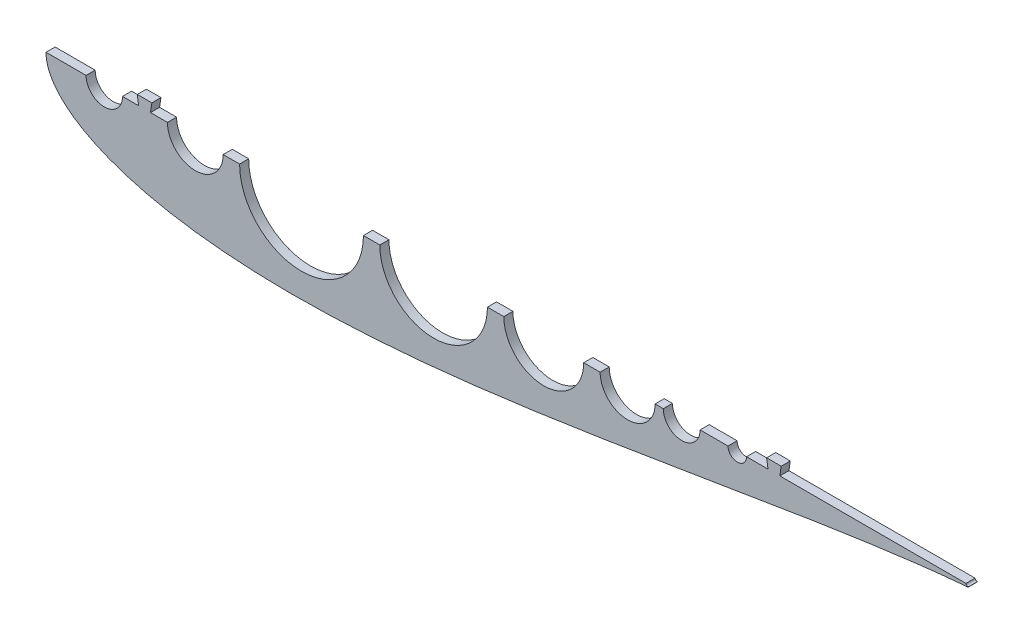
SolidWorks part; units mm, degrees
material "Beech"
ref_plane "Front Plane" through (0, 0, 0) normal (0, 0, 1) x (1, 0, 0)
ref_plane "Top Plane" through (0, 0, 0) normal (0, 1, 0) x (1, 0, 0)
ref_plane "Right Plane" through (0, 0, 0) normal (1, 0, 0) x (0, 0, -1)
curve "Curve4"
  spline degree 3 poles (100, 0, 0) (99.8498, 0.0023, 0) (99.4759, 0.008, 0) (99.1023, 0.0238, 0) (98.8789, 0.0332, 0) knots 0 0 0 0 0.401829 1 1 1 1
curve "Curve5"
  spline degree 3 poles (99.3714, -0.0082, 0) (100.2526, 0, 0) (99.3714, 0.0082, 0) (98.8504, 0.035, 0) (97.904, 0.0811, 0) (96.8285, 0.1543, 0) (95.5159, 0.2583, 0) (94.013, 0.3972, 0) (92.313, 0.574, 0) (90.4281, 0.791, 0) (88.3655, 1.0495, 0) (86.1348, 1.3497, 0) (83.7456, 1.691, 0) (81.2082, 2.0715, 0) (78.5335, 2.4886, 0) (75.7326, 2.9386, 0) (72.8172, 3.4168, 0) (69.799, 3.9177, 0) (66.6904, 4.435, 0) (63.5039, 4.9616, 0) (60.2521, 5.4899, 0) (56.948, 6.0119, 0) (53.6049, 6.519, 0) (50.2363, 7.0024, 0) (46.8558, 7.4534, 0) (43.4774, 7.8632, 0) (40.1152, 8.2232, 0) (36.7837, 8.5249, 0) (33.4975, 8.7606, 0) (30.2716, 8.923, 0) (27.1211, 9.0055, 0) (24.0614, 9.0025, 0) (21.108, 8.909, 0) (18.277, 8.7213, 0) (15.5843, 8.4369, 0) (13.0466, 8.0543, 0) (10.6806, 7.5735, 0) (8.5039, 6.996, 0) (6.5349, 6.3253, 0) (4.7933, 5.5673, 0) (3.3001, 4.7321, 0) (2.0777, 3.8366, 0) (1.1467, 2.91, 0) (0.5165, 2.0014, 0) (0.165, 1.1816, 0) (0.0231, 0.524, 0) (-0.0093, 0, 0) (0.0231, -0.524, 0) (0.165, -1.1816, 0) (0.5165, -2.0014, 0) (1.1467, -2.91, 0) (2.0777, -3.8366, 0) (3.3001, -4.7321, 0) (4.7933, -5.5673, 0) (6.5349, -6.3253, 0) (8.5039, -6.996, 0) (10.6806, -7.5735, 0) (13.0466, -8.0543, 0) (15.5843, -8.4369, 0) (18.277, -8.7213, 0) (21.108, -8.909, 0) (24.0614, -9.0025, 0) (27.1211, -9.0055, 0) (30.2716, -8.923, 0) (33.4975, -8.7606, 0) (36.7837, -8.5249, 0) (40.1152, -8.2232, 0) (43.4774, -7.8632, 0) (46.8558, -7.4534, 0) (50.2363, -7.0024, 0) (53.6049, -6.519, 0) (56.948, -6.0119, 0) (60.2521, -5.4899, 0) (63.5039, -4.9616, 0) (66.6904, -4.435, 0) (69.799, -3.9177, 0) (72.8172, -3.4168, 0) (75.7326, -2.9386, 0) (78.5335, -2.4886, 0) (81.2082, -2.0715, 0) (83.7456, -1.691, 0) (86.1348, -1.3497, 0) (88.3655, -1.0495, 0) (90.4281, -0.791, 0) (92.313, -0.574, 0) (94.013, -0.3972, 0) (95.5159, -0.2583, 0) (96.8285, -0.1543, 0) (97.904, -0.0811, 0) (98.8504, -0.035, 0) (99.3714, -0.0082, 0) (100.2526, 0, 0) (99.3714, 0.0082, 0) knots -0.009667 -0.005395 -0.002168 0 0.002168 0.005395 0.009667 0.014967 0.021271 0.028553 0.036781 0.04592 0.055932 0.066773 0.078397 0.090755 0.103793 0.117456 0.131686 0.146422 0.1616 0.177156 0.193024 0.209135 0.225421 0.241812 0.258238 0.274629 0.290914 0.307025 0.322893 0.338448 0.353626 0.368361 0.38259 0.396253 0.40929 0.421647 0.43327 0.444109 0.454119 0.463255 0.471479 0.478755 0.485052 0.490344 0.49461 0.497833 0.5 0.502167 0.50539 0.509656 0.514948 0.521245 0.528521 0.536745 0.545881 0.555891 0.56673 0.578353 0.59071 0.603747 0.61741 0.631639 0.646374 0.661552 0.677107 0.692975 0.709086 0.725371 0.741762 0.758188 0.774579 0.790865 0.806976 0.822844 0.8384 0.853578 0.868314 0.882544 0.896207 0.909245 0.921603 0.933227 0.944068 0.95408 0.963219 0.971447 0.978729 0.985033 0.990333 0.994605 0.997832 1 1.002168 1.005395 1.009667 periodic
sketch "Sketch2" plane through (0, 0, 0) normal (0, 0, 1) x (1, 0, 0)
  line L0 (100, 0) -> (0, 0) construction
  line L1 (1.2169, -991.9959) -> (1.2169, 49008.0041) construction
  line L2 (84.709, 0) -> (123.571, 0) construction
  line L3 (125.634, 0) -> (131.6629, 0) construction
  line L4 (643.5991, 0) -> (643.5991, -1.016)
  line L9 (0, 0) -> (643.9668, 0)
  line L13 (460.661, 0) -> (473.361, 0)
  circle A0 centre (104.14, 0) radius 19.431 construction
  arc A1 (1.2169, -4.6585) -> (1.2169, 4.6585) centre (9.525, 0) cw
  arc A2 (641.5671, 0) -> (644.1071, 0) centre (642.8371, 0) ccw
  circle A4 centre (104.14, 0) radius 19.431
  circle A9 centre (40.64, 0) radius 12.7
  circle A14 centre (642.3793, 0) radius 1.5875 construction
  arc A15 (642.5108, -1.582) -> (642.5108, 1.582) centre (642.3793, 0) ccw
  spline S2 degree 3 poles (666.3448, -0.0547) (672.2538, 0) (666.3448, 0.0547) (662.8509, 0.2344) (656.505, 0.5436) (649.293, 1.0348) (640.4916, 1.7319) (630.4138, 2.6634) (619.0141, 3.8493) (606.375, 5.3044) (592.5439, 7.0376) (577.5855, 9.0506) (561.5643, 11.3389) (544.5497, 13.8907) (526.6141, 16.6877) (507.8326, 19.7051) (488.2827, 22.9117) (468.0444, 26.2704) (447.1994, 29.739) (425.8316, 33.2703) (404.0263, 36.8132) (381.8707, 40.3133) (359.4533, 43.7135) (336.8645, 46.9554) (314.1962, 49.9798) (291.5418, 52.7277) (268.9963, 55.1412) (246.6566, 57.1646) (224.6209, 58.7452) (202.9892, 59.8341) (181.8631, 60.3875) (161.3458, 60.367) (141.542, 59.7399) (122.5581, 58.4818) (104.5023, 56.5743) (87.485, 54.0089) (71.6197, 50.7848) (57.0237, 46.9125) (43.8205, 42.415) (32.1416, 37.3322) (22.1291, 31.7315) (13.9324, 25.7264) (7.6896, 19.5132) (3.4631, 13.4204) (1.1063, 7.9234) (0.1546, 3.5138) (-0.0622, 0) (0.1546, -3.5138) (1.1063, -7.9234) (3.4631, -13.4204) (7.6896, -19.5132) (13.9324, -25.7264) (22.1291, -31.7315) (32.1416, -37.3322) (43.8205, -42.415) (57.0237, -46.9125) (71.6197, -50.7848) (87.485, -54.0089) (104.5023, -56.5743) (122.5581, -58.4818) (141.542, -59.7399) (161.3458, -60.367) (181.8631, -60.3875) (202.9892, -59.8341) (224.6209, -58.7452) (246.6566, -57.1646) (268.9963, -55.1412) (291.5418, -52.7277) (314.1962, -49.9798) (336.8645, -46.9554) (359.4533, -43.7135) (381.8707, -40.3133) (404.0263, -36.8132) (425.8316, -33.2703) (447.1994, -29.739) (468.0444, -26.2704) (488.2827, -22.9117) (507.8326, -19.7051) (526.6141, -16.6877) (544.5497, -13.8907) (561.5643, -11.3389) (577.5855, -9.0506) (592.5439, -7.0376) (606.375, -5.3044) (619.0141, -3.8493) (630.4138, -2.6634) (640.4916, -1.7319) (649.293, -1.0348) (656.505, -0.5436) (662.8509, -0.2344) (666.3448, -0.0547) (672.2538, 0) (666.3448, 0.0547) knots -0.009667 -0.005395 -0.002168 0 0.002168 0.005395 0.009667 0.014967 0.021271 0.028553 0.036781 0.04592 0.055932 0.066773 0.078397 0.090755 0.103793 0.117456 0.131686 0.146422 0.1616 0.177156 0.193024 0.209135 0.225421 0.241812 0.258238 0.274629 0.290914 0.307025 0.322893 0.338448 0.353626 0.368361 0.38259 0.396253 0.40929 0.421647 0.43327 0.444109 0.454119 0.463255 0.471479 0.478755 0.485052 0.490344 0.49461 0.497833 0.5 0.502167 0.50539 0.509656 0.514948 0.521245 0.528521 0.536745 0.545881 0.555891 0.56673 0.578353 0.59071 0.603747 0.61741 0.631639 0.646374 0.661552 0.677107 0.692975 0.709086 0.725371 0.741762 0.758188 0.774579 0.790865 0.806976 0.822844 0.8384 0.853578 0.868314 0.882544 0.896207 0.909245 0.921603 0.933227 0.944068 0.95408 0.963219 0.971447 0.978729 0.985033 0.990333 0.994605 0.997832 1 1.002168 1.005395 1.009667 only from (670.56, 0) to (670.56, 0)
  point P2 (167.64, 0)
  point P8 (1.2169, -4.6585)
  point P10 (1.2169, 4.6585)
  point P28 (133.9182, 0)
  point P49 (130.0977, 0)
  point P59 (95.1064, 0)
  dimension "D2" = 38.862
  dimension "D3" = 1.016
  dimension "D4" = 1.27
  dimension "D8" = 25.4
  dimension "D9" = 63.5
  dimension "D10" = 3.175
  dimension "D1" = 167.64
  dimension "D6" = 63.5
extrude "Boss-Extrude1" add sketch "Sketch2" along normal blind 6.35
sketch "Sketch3" plane through (0, 0, 6.35) normal (0, 0, 1) x (1, 0, 0)
  line L0 (84.14, -12.7) -> (62.637, -12.7) construction
  line L1 (430.4749, -1041.2705) -> (430.4749, 48958.7295) construction
  line L2 (123.571, 0) -> (641.5671, 0) construction
  line L3 (27.94, 0) -> (0, 0)
  line L4 (641.5671, 0) -> (123.571, 0)
  line L5 (84.709, 0) -> (53.34, 0)
  line L6 (27.94, 0) -> (0, 0)
  line L7 (221.3683, -1000) -> (221.3683, 49000) construction
  line L8 (84.709, 0) -> (53.34, 0)
  line L9 (232.7983, -1000) -> (232.7983, 49000) construction
  line L10 (307.8396, -1000) -> (307.8396, 49000) construction
  line L11 (319.2696, -1000) -> (319.2696, 49000) construction
  line L12 (374.9948, -1000) -> (374.9948, 49000) construction
  line L13 (84.709, -17.145) -> (65.0689, -17.145) construction
  line L14 (424.7788, -1000) -> (424.7788, 49000) construction
  line L15 (135.001, -1000) -> (135.001, 49000) construction
  line L16 (386.4248, -1000) -> (386.4248, 49000) construction
  line L17 (52.7726, -27.2676) -> (52.7726, -27.2676) construction
  arc A0 (36.4352, -25.0495) -> (62.637, -12.7) centre (40.64, 0) ccw construction
  circle A2 centre (178.1847, 0) radius 43.1837
  arc A3 (642.5108, -1.582) -> (643.5991, -1.016) centre (642.3793, 0) ccw
  arc A4 (84.709, 0) -> (123.571, 0) centre (104.14, 0) ccw
  arc A5 (27.94, 0) -> (53.34, 0) centre (40.64, 0) ccw
  arc A6 (642.5108, -1.582) -> (643.5991, -1.016) centre (642.3793, 0) ccw
  circle A7 centre (270.319, 0) radius 37.5206
  arc A8 (27.94, 0) -> (53.34, 0) centre (40.64, 0) ccw
  circle A9 centre (347.1322, 0) radius 27.8626
  circle A10 centre (405.6018, 0) radius 19.177
  circle A11 centre (443.3019, 0) radius 12.827
  circle A12 centre (482.0825, 0) radius 6.477
  arc A13 (52.7726, -27.2676) -> (65.0689, -17.145) centre (40.64, 0) ccw construction
  arc A14 (638.2053, 15.2585) -> (638.2053, 15.2585) centre (638.2053, 15.2585) ccw construction
  arc A18 (641.5671, 0) -> (643.5991, -1.016) centre (642.8371, 0) ccw
  arc A19 (641.5671, 0) -> (643.5991, -1.016) centre (642.8371, 0) ccw
  spline S1 degree 3 poles (1083.539, -1665.6175) (237.9838, 156.2926) (-13.4194, 59.3783) (1.1063, -7.9234) (3.4631, -13.4204) (7.6896, -19.5132) (13.9324, -25.7264) (22.1291, -31.7315) (32.1416, -37.3322) (43.8205, -42.415) (57.0237, -46.9125) (71.6197, -50.7848) (87.485, -54.0089) (104.5023, -56.5743) (122.5581, -58.4818) (141.542, -59.7399) (161.3458, -60.367) (181.8631, -60.3875) (202.9892, -59.8341) (224.6209, -58.7452) (246.6566, -57.1646) (268.9963, -55.1412) (291.5418, -52.7277) (314.1962, -49.9798) (336.8645, -46.9554) (359.4533, -43.7135) (381.8707, -40.3133) (404.0263, -36.8132) (425.8316, -33.2703) (447.1994, -29.739) (468.0444, -26.2704) (488.2827, -22.9117) (507.8326, -19.7051) (526.6141, -16.6877) (544.5497, -13.8907) (561.5643, -11.3389) (577.5855, -9.0506) (592.5439, -7.0376) (606.375, -5.3044) (619.0141, -3.8493) (630.4138, -2.6634) (741.1247, 7.5694) (864.0226, -5.3554) (-1347.5502, -198.2161) knots 0.362281 0.362281 0.362281 0.362281 0.502167 0.50539 0.509656 0.514948 0.521245 0.528521 0.536745 0.545881 0.555891 0.56673 0.578353 0.59071 0.603747 0.61741 0.631639 0.646374 0.661552 0.677107 0.692975 0.709086 0.725371 0.741762 0.758188 0.774579 0.790865 0.806976 0.822844 0.8384 0.853578 0.868314 0.882544 0.896207 0.909245 0.921603 0.933227 0.944068 0.95408 0.963219 0.971447 0.978729 1.20286 1.20286 1.20286 1.20286 only from (0, 0) to (642.5108, -1.582)
  spline S2 degree 3 poles (0, 0) (0, -1.0075) (0.1546, -3.5138) (1.1063, -7.9234) (3.4631, -13.4204) (7.6896, -19.5132) (13.9324, -25.7264) (22.1291, -31.7315) (32.1416, -37.3322) (43.8205, -42.415) (57.0237, -46.9125) (71.6197, -50.7848) (87.485, -54.0089) (104.5023, -56.5743) (122.5581, -58.4818) (141.542, -59.7399) (161.3458, -60.367) (181.8631, -60.3875) (202.9892, -59.8341) (224.6209, -58.7452) (246.6566, -57.1646) (268.9963, -55.1412) (291.5418, -52.7277) (314.1962, -49.9798) (336.8645, -46.9554) (359.4533, -43.7135) (381.8707, -40.3133) (404.0263, -36.8132) (425.8316, -33.2703) (447.1994, -29.739) (468.0444, -26.2704) (488.2827, -22.9117) (507.8326, -19.7051) (526.6141, -16.6877) (544.5497, -13.8907) (561.5643, -11.3389) (577.5855, -9.0506) (592.5439, -7.0376) (606.375, -5.3044) (619.0141, -3.8493) (630.4138, -2.6634) (638.0937, -1.9535) (641.9934, -1.6251) (642.5108, -1.582) knots 0.5 0.5 0.5 0.5 0.502167 0.50539 0.509656 0.514948 0.521245 0.528521 0.536745 0.545881 0.555891 0.56673 0.578353 0.59071 0.603747 0.61741 0.631639 0.646374 0.661552 0.677107 0.692975 0.709086 0.725371 0.741762 0.758188 0.774579 0.790865 0.806976 0.822844 0.8384 0.853578 0.868314 0.882544 0.896207 0.909245 0.921603 0.933227 0.944068 0.95408 0.963219 0.971447 0.978729 0.979843 0.979843 0.979843 0.979843
  spline S4 degree 1 poles (52.7726, -27.2676) (638.2053, 15.2585) knots 0 0 1 1 construction
  spline S5 degree 3 poles (52.7726, -27.2676) (54.098, -27.7509) (56.7529, -28.6784) (62.1794, -30.4243) (69.1006, -32.3953) (77.5892, -34.4571) (89.0862, -36.8389) (103.7331, -39.1926) (127.5352, -41.8455) (149.5112, -42.9751) (171.6139, -43.2629) (184.6425, -43.1469) (205.1644, -42.6052) (230.9293, -41.2613) (259.7939, -38.828) (285.4834, -36.1555) (308.0659, -33.4851) (336.7822, -29.6913) (372.3922, -24.4911) (406.8647, -19.0063) (435.2357, -14.3425) (451.6826, -11.6119) (464.2574, -9.5208) (476.8398, -7.4307) (497.3171, -4.0443) (526.9629, 0.7645) (562.929, 6.2684) (594.1055, 10.5252) (616.0859, 13.0867) (628.694, 14.3901) (635.0364, 14.9826) (638.2053, 15.2585) knots 0.548481 0.548481 0.548481 0.548481 0.551835 0.555189 0.561898 0.568606 0.575315 0.588731 0.602148 0.628982 0.637543 0.65096 0.657668 0.682649 0.707463 0.72088 0.738887 0.756894 0.783728 0.816817 0.832298 0.845715 0.852722 0.859728 0.873145 0.897318 0.924152 0.950985 0.964402 0.971111 0.977819 0.977819 0.977819 0.977819 construction
  line M19 (641.5671, 0) -> (123.571, 0)
  dimension "D3" = 11.43
  dimension "D7" = 38.354
  dimension "D8" = 25.654
  dimension "D9" = 12.954
  dimension "D4" = 11.43
  dimension "D5" = 11.43
  dimension "D6" = 11.43
  dimension "D1" = 0
  dimension "D10" = 17.145
extrude "Cut-Extrude2" cut sketch "Sketch3" against normal through all both and the other way through all contours A2 M19 | A7 M19 | A9 M19 | A10 M19 | A11 M19 | A12 M19
sketch "Sketch4" plane through (0, 0, 6.35) normal (0, 0, 1) x (1, 0, 0)
  line L0 (63.66, 6.35) -> (73.82, 6.35)
  line L1 (65.565, 6.35) -> (71.915, 6.35)
  line L2 (65.565, 6.35) -> (65.565, -6.35)
  line L3 (65.565, -6.35) -> (71.915, -6.35)
  line L4 (71.915, 6.35) -> (71.915, -6.35)
  line L5 (65.565, 6.35) -> (71.915, -6.35) construction
  line L6 (65.565, -6.35) -> (71.915, 6.35) construction
  line L7 (71.915, -6.35) -> (73.82, 6.35)
  line L8 (63.66, 6.35) -> (65.565, -6.35)
  line L9 (232.7983, 0) -> (221.3683, 0)
  line L18 (232.7983, 0) -> (221.3683, 0)
  line L20 (135.001, 0) -> (123.571, 0)
  line L21 (135.001, 0) -> (123.571, 0)
  line L22 (84.709, 0) -> (53.34, 0)
  line L23 (84.709, 0) -> (53.34, 0)
  line L24 (27.94, 0) -> (0, 0)
  line L25 (27.94, 0) -> (0, 0)
  line L26 (641.5671, 0) -> (488.5595, 0)
  line L27 (502.5295, 6.35) -> (512.6895, 6.35)
  line L28 (504.4345, 6.35) -> (510.7845, 6.35)
  line L29 (504.4345, 6.35) -> (504.4345, -6.35)
  line L30 (504.4345, -6.35) -> (510.7845, -6.35)
  line L31 (510.7845, 6.35) -> (510.7845, -6.35)
  line L32 (504.4345, 6.35) -> (510.7845, -6.35) construction
  line L33 (504.4345, -6.35) -> (510.7845, 6.35) construction
  line L34 (504.4345, -6.35) -> (502.5295, 6.35)
  line L35 (510.7845, -6.35) -> (512.6895, 6.35)
  line L36 (641.5671, 0) -> (488.5595, 0)
  line L37 (475.6055, 0) -> (456.1289, 0)
  line L38 (475.6055, 0) -> (456.1289, 0)
  line L39 (430.4749, 0) -> (424.7788, 0)
  line L40 (430.4749, 0) -> (424.7788, 0)
  line L41 (386.4248, 0) -> (374.9948, 0)
  line L42 (386.4248, 0) -> (374.9948, 0)
  line L43 (319.2696, 0) -> (307.8396, 0)
  line L44 (319.2696, 0) -> (307.8396, 0)
  arc A9 (232.7983, 0) -> (307.8396, 0) centre (270.319, 0) ccw
  arc A10 (232.7983, 0) -> (307.8396, 0) centre (270.319, 0) ccw
  arc A11 (135.001, 0) -> (221.3683, 0) centre (178.1847, 0) ccw
  arc A12 (135.001, 0) -> (221.3683, 0) centre (178.1847, 0) ccw
  arc A13 (84.709, 0) -> (123.571, 0) centre (104.14, 0) ccw
  arc A14 (84.709, 0) -> (123.571, 0) centre (104.14, 0) ccw
  arc A15 (27.94, 0) -> (53.34, 0) centre (40.64, 0) ccw
  arc A16 (386.4248, 0) -> (424.7788, 0) centre (405.6018, 0) ccw
  arc A17 (27.94, 0) -> (53.34, 0) centre (40.64, 0) ccw
  arc A18 (642.5108, -1.582) -> (643.5991, -1.016) centre (642.3793, 0) ccw
  arc A19 (642.5108, -1.582) -> (643.5991, -1.016) centre (642.3793, 0) ccw
  arc A20 (475.6055, 0) -> (488.5595, 0) centre (482.0825, 0) ccw
  arc A21 (475.6055, 0) -> (488.5595, 0) centre (482.0825, 0) ccw
  arc A22 (430.4749, 0) -> (456.1289, 0) centre (443.3019, 0) ccw
  arc A23 (430.4749, 0) -> (456.1289, 0) centre (443.3019, 0) ccw
  arc A24 (319.2696, 0) -> (374.9948, 0) centre (347.1322, 0) ccw
  arc A25 (386.4248, 0) -> (424.7788, 0) centre (405.6018, 0) ccw
  arc A26 (319.2696, 0) -> (374.9948, 0) centre (347.1322, 0) ccw
  arc A28 (641.5671, 0) -> (643.5991, -1.016) centre (642.8371, 0) ccw
  arc A29 (641.5671, 0) -> (643.5991, -1.016) centre (642.8371, 0) ccw
  spline S1 degree 3 poles (1083.539, -1665.6175) (237.9838, 156.2926) (-13.4194, 59.3783) (1.1063, -7.9234) (3.4631, -13.4204) (7.6896, -19.5132) (13.9324, -25.7264) (22.1291, -31.7315) (32.1416, -37.3322) (43.8205, -42.415) (57.0237, -46.9125) (71.6197, -50.7848) (87.485, -54.0089) (104.5023, -56.5743) (122.5581, -58.4818) (141.542, -59.7399) (161.3458, -60.367) (181.8631, -60.3875) (202.9892, -59.8341) (224.6209, -58.7452) (246.6566, -57.1646) (268.9963, -55.1412) (291.5418, -52.7277) (314.1962, -49.9798) (336.8645, -46.9554) (359.4533, -43.7135) (381.8707, -40.3133) (404.0263, -36.8132) (425.8316, -33.2703) (447.1994, -29.739) (468.0444, -26.2704) (488.2827, -22.9117) (507.8326, -19.7051) (526.6141, -16.6877) (544.5497, -13.8907) (561.5643, -11.3389) (577.5855, -9.0506) (592.5439, -7.0376) (606.375, -5.3044) (619.0141, -3.8493) (630.4138, -2.6634) (741.1247, 7.5694) (864.0226, -5.3554) (-1347.5502, -198.2161) knots 0.362281 0.362281 0.362281 0.362281 0.502167 0.50539 0.509656 0.514948 0.521245 0.528521 0.536745 0.545881 0.555891 0.56673 0.578353 0.59071 0.603747 0.61741 0.631639 0.646374 0.661552 0.677107 0.692975 0.709086 0.725371 0.741762 0.758188 0.774579 0.790865 0.806976 0.822844 0.8384 0.853578 0.868314 0.882544 0.896207 0.909245 0.921603 0.933227 0.944068 0.95408 0.963219 0.971447 0.978729 1.20286 1.20286 1.20286 1.20286 only from (0, 0) to (642.5108, -1.582)
  spline S2 degree 3 poles (0, 0) (0, -1.0075) (0.1546, -3.5138) (1.1063, -7.9234) (3.4631, -13.4204) (7.6896, -19.5132) (13.9324, -25.7264) (22.1291, -31.7315) (32.1416, -37.3322) (43.8205, -42.415) (57.0237, -46.9125) (71.6197, -50.7848) (87.485, -54.0089) (104.5023, -56.5743) (122.5581, -58.4818) (141.542, -59.7399) (161.3458, -60.367) (181.8631, -60.3875) (202.9892, -59.8341) (224.6209, -58.7452) (246.6566, -57.1646) (268.9963, -55.1412) (291.5418, -52.7277) (314.1962, -49.9798) (336.8645, -46.9554) (359.4533, -43.7135) (381.8707, -40.3133) (404.0263, -36.8132) (425.8316, -33.2703) (447.1994, -29.739) (468.0444, -26.2704) (488.2827, -22.9117) (507.8326, -19.7051) (526.6141, -16.6877) (544.5497, -13.8907) (561.5643, -11.3389) (577.5855, -9.0506) (592.5439, -7.0376) (606.375, -5.3044) (619.0141, -3.8493) (630.4138, -2.6634) (638.0937, -1.9535) (641.9934, -1.6251) (642.5108, -1.582) knots 0.5 0.5 0.5 0.5 0.502167 0.50539 0.509656 0.514948 0.521245 0.528521 0.536745 0.545881 0.555891 0.56673 0.578353 0.59071 0.603747 0.61741 0.631639 0.646374 0.661552 0.677107 0.692975 0.709086 0.725371 0.741762 0.758188 0.774579 0.790865 0.806976 0.822844 0.8384 0.853578 0.868314 0.882544 0.896207 0.909245 0.921603 0.933227 0.944068 0.95408 0.963219 0.971447 0.978729 0.979843 0.979843 0.979843 0.979843
  point P0 (68.74, 0)
  point P15 (68.74, 6.35)
  point P25 (68.74, 6.35)
  point P37 (507.6095, 0)
  point P44 (507.6095, 6.35)
  point P45 (507.6095, 6.35)
  line M32 (84.709, 0) -> (53.34, 0)
  dimension "D2" = 6.35
  dimension "D3" = 10.16
  dimension "D4" = 12.7
  dimension "D5" = 6.35
  dimension "D6" = 12.7
  dimension "D7" = 19.05
  dimension "D8" = 10.16
  dimension "D1" = 0
extrude "Boss-Extrude2" add sketch "Sketch4" against normal up to surface (6.35 mm away) contours L34 L36 L29 L27 | L31 L27 L29 L36 | L36 L35 L27 L31 | L0 L8 L2 M32 | L4 L0 L2 M32 | L7 L0 L4 M32 up to face at (307.4484, -9.0862, 0)
equation "\"0.5n\"=0"
